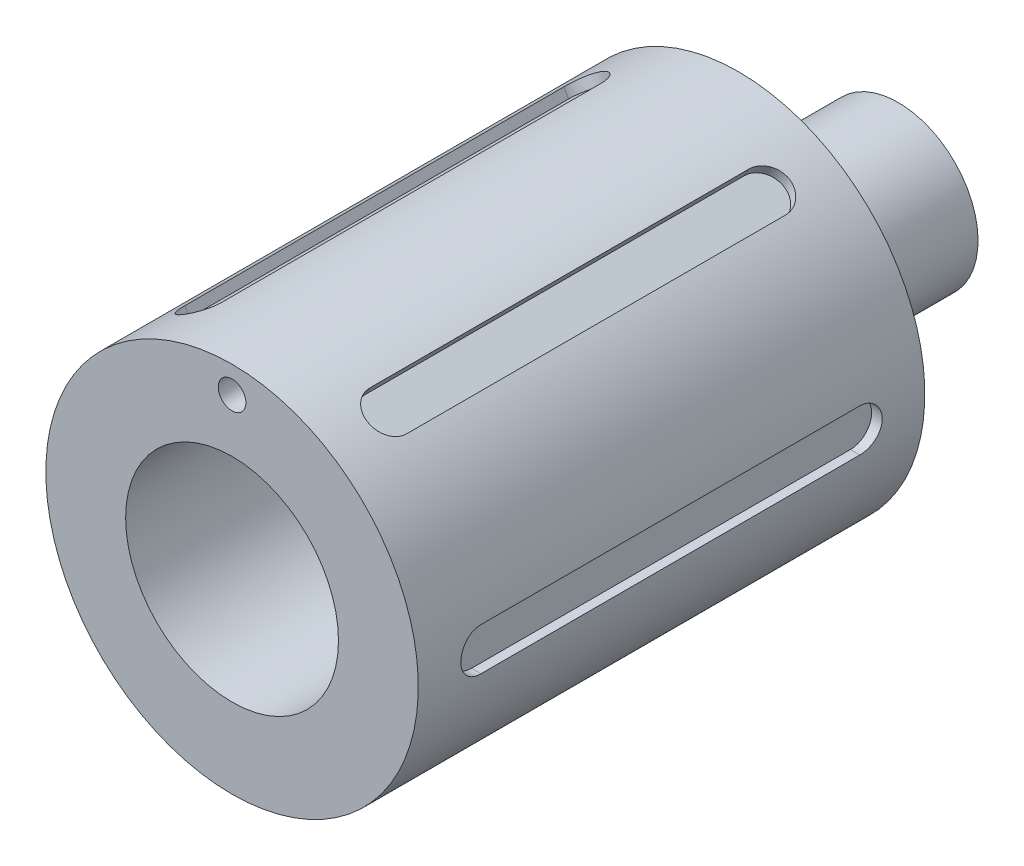
SolidWorks part; units mm, degrees
material "Plain Carbon Steel"
ref_plane "Front" through (0, 0, 0) normal (0, 0, 1) x (1, 0, 0)
ref_plane "Top" through (0, 0, 0) normal (0, 1, 0) x (1, 0, 0)
ref_plane "Right" through (0, 0, 0) normal (1, 0, 0) x (0, 0, -1)
sketch "Sketch1" plane through (0, 0, 0) normal (1, 0, 0) x (0, 0, -1)
  line L0 (0, 22.225) -> (60.452, 22.225)
  line L1 (60.452, 22.225) -> (60.452, 9.525)
  line L2 (60.452, 9.525) -> (79.502, 9.525)
  line L3 (79.502, 9.525) -> (79.502, 0)
  line L4 (79.502, 0) -> (57.15, 0)
  line L5 (57.15, 0) -> (57.15, 12.7)
  line L6 (57.15, 12.7) -> (0, 12.7)
  line L7 (0, 12.7) -> (0, 22.225)
  line L8 (0, 0) -> (57.15, 0) construction
  dimension "D1" = 19.05
  dimension "D2" = 44.45
  dimension "D3" = 25.4
  dimension "D4" = 57.15
  dimension "D5" = 60.452
  dimension "D6" = 19.05
revolve "Revolve1" add sketch "Sketch1" angle 360 about L8
ref_plane "Plane1" through (22.225, 0, 0) normal (1, 0, 0) x (0, 0, -1)
sketch "Sketch2" plane through (22.225, 0, 0) normal (1, 0, 0) x (0, 0, -1)
  line L0 (7.62, 0) -> (52.832, 0) construction
  line L1 (7.62, 2.54) -> (52.832, 2.54)
  line L2 (7.62, -2.54) -> (52.832, -2.54)
  arc A0 (7.62, 2.54) -> (7.62, -2.54) centre (7.62, 0) ccw
  arc A1 (52.832, -2.54) -> (52.832, 2.54) centre (52.832, 0) ccw
  point P2 (30.226, 0)
  dimension "D1" = 2.54
  dimension "D2" = 7.62
  dimension "D3" = 45.212
extrude "Cut-Extrude1" cut sketch "Sketch2" against normal blind 1.27
pattern_circular "CirPattern1" count 6 over 360 about axis through (0, 0, 0) along (0, 0, 1) of "Cut-Extrude1"
hole_wizard "1/8 (0.13) Diameter Hole1" positions "Sketch4" profile "Sketch5" hole size "1/8" standard "ANSI Inch"
sketch "Sketch4" plane through (0, 0, 0) normal (0, 0, 1) x (1, 0, 0)
  point P0 (0, 19.05)
  dimension "D1" = 19.05
sketch "Sketch5" plane through (0, 19.05, 0) normal (1, 0, 0) x (0, -1, 0)
  line L0 (0, 0) -> (0, 16.867)
  line L1 (0, 16.867) -> (1.651, 15.875)
  line L2 (1.651, 15.875) -> (1.651, 0)
  line L5 (1.651, 0) -> (0, 0)
  line L10 (0, 16.867) -> (-1.651, 15.875) construction
  line L11 (0, -6.35) -> (0, 107.95) construction
  dimension "Hole Dia." = 3.302
  dimension "Hole Depth" = 15.875
  dimension "Drill Angle" = 118
